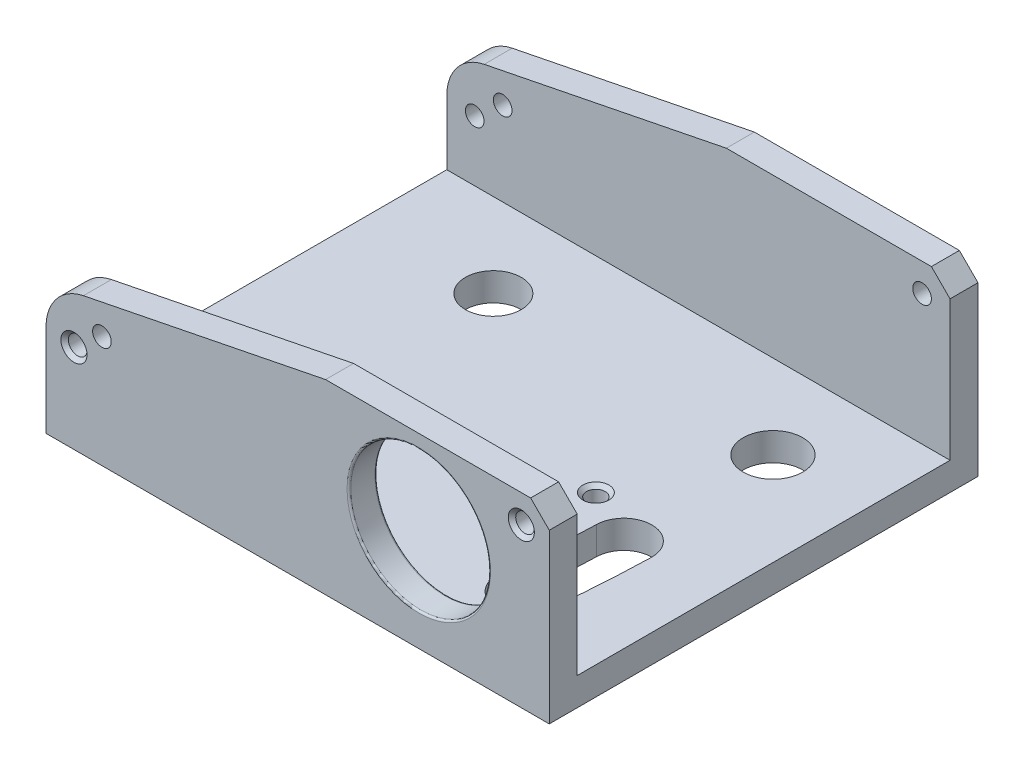
SolidWorks part; units mm, degrees
material "6061 Alloy"
ref_plane "Front Plane" through (0, 0, 0) normal (0, 0, 1) x (1, 0, 0)
ref_plane "Top Plane" through (0, 0, 0) normal (0, 1, 0) x (1, 0, 0)
ref_plane "Right Plane" through (0, 0, 0) normal (1, 0, 0) x (0, 0, -1)
sketch "Sketch1" plane through (0, 0, 0) normal (0, 1, 0) x (1, 0, 0)
  line L0 (0, 0) -> (-70, 0) construction
  line L1 (-22, 6) -> (5, 6)
  line L2 (-22, 6) -> (-22, -17)
  line L3 (-22, -17) -> (5, -17)
  line L4 (5, 6) -> (5, -17)
  line L5 (-70, 0) -> (-70, -6) construction
  circle A0 centre (0, 0) radius 1.6
  arc A1 (-1.8147, -12.8501) -> (-1.4994, -7.9572) centre (-70, -6) ccw
  arc A2 (1.1703, -13.1499) -> (1.4994, -8.0428) centre (-70, -6) ccw
  arc A3 (-1.4994, -7.9572) -> (1.4994, -8.0428) centre (0, -8) cw
  arc A4 (1.1703, -13.1499) -> (-1.8147, -12.8501) centre (-0.3222, -13) cw
  circle A5 centre (-15, 0) radius 1.5
  circle A6 centre (-15, 0) radius 3 construction
  circle A7 centre (-3, -6.5) radius 0.5
  dimension "D1" = 3.2
  dimension "D8" = 1.5
  dimension "D11" = 3
  dimension "D13" = 6
  dimension "D14" = 1
  dimension "D2" = 27
  dimension "D3" = 6
  dimension "D4" = 23
  dimension "D5" = 5
  dimension "D6" = 6
  dimension "D7" = 70
  dimension "D9" = 8
  dimension "D10" = 13
  dimension "D12" = 15
  dimension "D15" = 6.5
  dimension "D16" = 3
extrude "Extrude1" add sketch "Sketch1" along normal blind 1.5
sketch "Sketch2" plane through (0, 0, 17) normal (0, 0, 1) x (1, 0, 0)
  line L0 (-22, 1.5) -> (5, 1.5)
  line L1 (5, 1.5) -> (5, 9)
  line L2 (5, 9) -> (4, 10)
  line L3 (4, 10) -> (-7, 10)
  line L4 (-7, 10) -> (-22, 7)
  line L5 (-22, 7) -> (-22, 1.5)
  line L6 (-22, 0) -> (5, 0) construction
  line L7 (-20.5, 4.75) -> (-19, 6) construction
  line L8 (-22, 3.5) -> (-19, 3.5) construction
  circle A0 centre (3.5, 8.5) radius 0.5
  circle A1 centre (-2, 5.5) radius 3.75
  circle A2 centre (-20.5, 4.75) radius 0.5
  circle A3 centre (-19, 6) radius 0.5
  circle A4 centre (-20.5, 4.75) radius 1.25 construction
  dimension "D6" = 1
  dimension "D9" = 7.5
  dimension "D14" = 1
  dimension "D15" = 1
  dimension "D17" = 2.5
  dimension "D2" = 1
  dimension "D3" = 1
  dimension "D4" = 10
  dimension "D5" = 12
  dimension "D7" = 1.5
  dimension "D8" = 1.5
  dimension "D10" = 5.5
  dimension "D11" = 7
  dimension "D12" = 1.5
  dimension "D13" = 4.75
  dimension "D16" = 1.5
  dimension "D18" = 7
  dimension "D19" = 2
  dimension "D20" = 6
  dimension "D21" = 1.25
extrude "Extrude2" add sketch "Sketch2" against normal blind 1.5
sketch "Sketch3" plane through (0, 0, -6) normal (0, 0, -1) x (-1, 0, 0)
  line L0 (-5, 1.5) -> (22, 1.5)
  line L1 (22, 1.5) -> (22, 7)
  line L2 (22, 7) -> (7, 10)
  line L3 (7, 10) -> (-4, 10)
  line L4 (-4, 10) -> (-5, 9)
  line L5 (-5, 9) -> (-5, 1.5)
  circle A0 centre (-3.5, 8.5) radius 0.5
  circle A1 centre (-3.5, 8.5) radius 0.5 construction
  circle A2 centre (20.5, 4.75) radius 0.5
  circle A3 centre (20.5, 4.75) radius 0.5 construction
  circle A4 centre (19, 6) radius 0.5
  circle A5 centre (19, 6) radius 0.5 construction
extrude "Extrude3" add sketch "Sketch3" against normal blind 1.5
fillet "Fillet1" radius 0.1 2 edges at (1.75, 5.5, 17) (1.75, 5.5, 15.5)
chamfer "Chamfer1" distance 0.2 angle 45 6 edges at (-20, 4.75, 17) (4, 8.5, 17) (3, 8.5, -6) (-21, 4.75, -6) (-3, 0, 7) (-3, 1.5, 7)
fillet "Fillet2" radius 2.5 2 edges at (-22, 7, 16.25) (-22, 7, -5.25)
